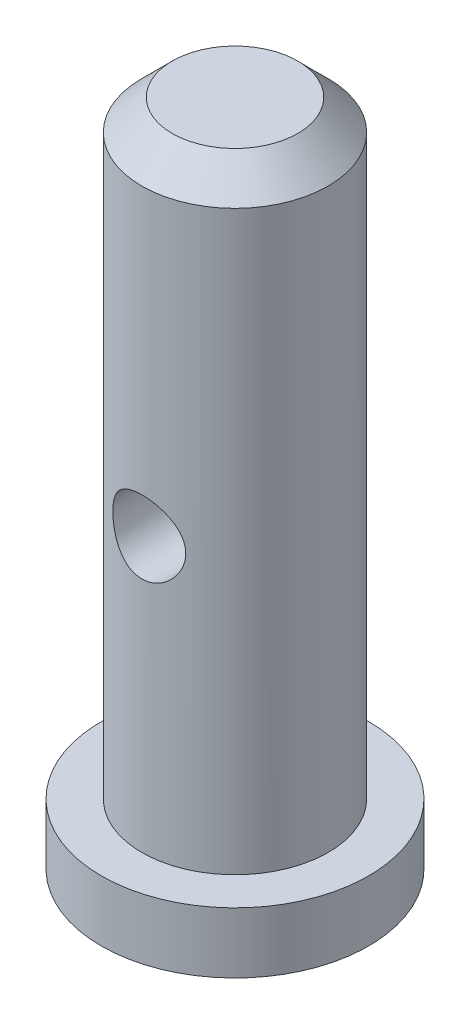
SolidWorks part; units mm, degrees
ref_plane "Front Plane" through (0, 0, 0) normal (0, 0, 1) x (1, 0, 0)
ref_plane "Top Plane" through (0, 0, 0) normal (0, 1, 0) x (1, 0, 0)
ref_plane "Right Plane" through (0, 0, 0) normal (1, 0, 0) x (0, 0, -1)
sketch "Sketch1" plane through (0, 0, 0) normal (0, 0, 1) x (1, 0, 0)
  line L0 (0, 0) -> (0, 16.5) construction
  line L1 (0, 16.5) -> (2.3, 16.5)
  line L2 (2.3, 16.5) -> (2.3, 1.5)
  line L3 (2.3, 1.5) -> (3.3, 1.5)
  line L4 (3.3, 1.5) -> (3.3, 0)
  line L5 (3.3, 0) -> (0, 0)
  line L6 (0, 0) -> (0, 16.5)
  dimension "D1" = 2.3
  dimension "D2" = 1.5
  dimension "D3" = 1
  dimension "D4" = 15
revolve "Revolve1" add sketch "Sketch1" angle 360 about L0
chamfer "Chamfer1" distance 0.75 angle 45 1 edges at (0, 16.5, -2.3)
sketch "Sketch2" plane through (0, 0, 0) normal (0, 0, 1) x (1, 0, 0)
  line L0 (3.3, 1.5) -> (-3.3, 1.5) construction
  circle A0 centre (0, 8.25) radius 0.9
  dimension "D2" = 1.8
  dimension "D1" = 6.75
extrude "Cut-Extrude1" cut sketch "Sketch2" against normal through all both and the other way through all
